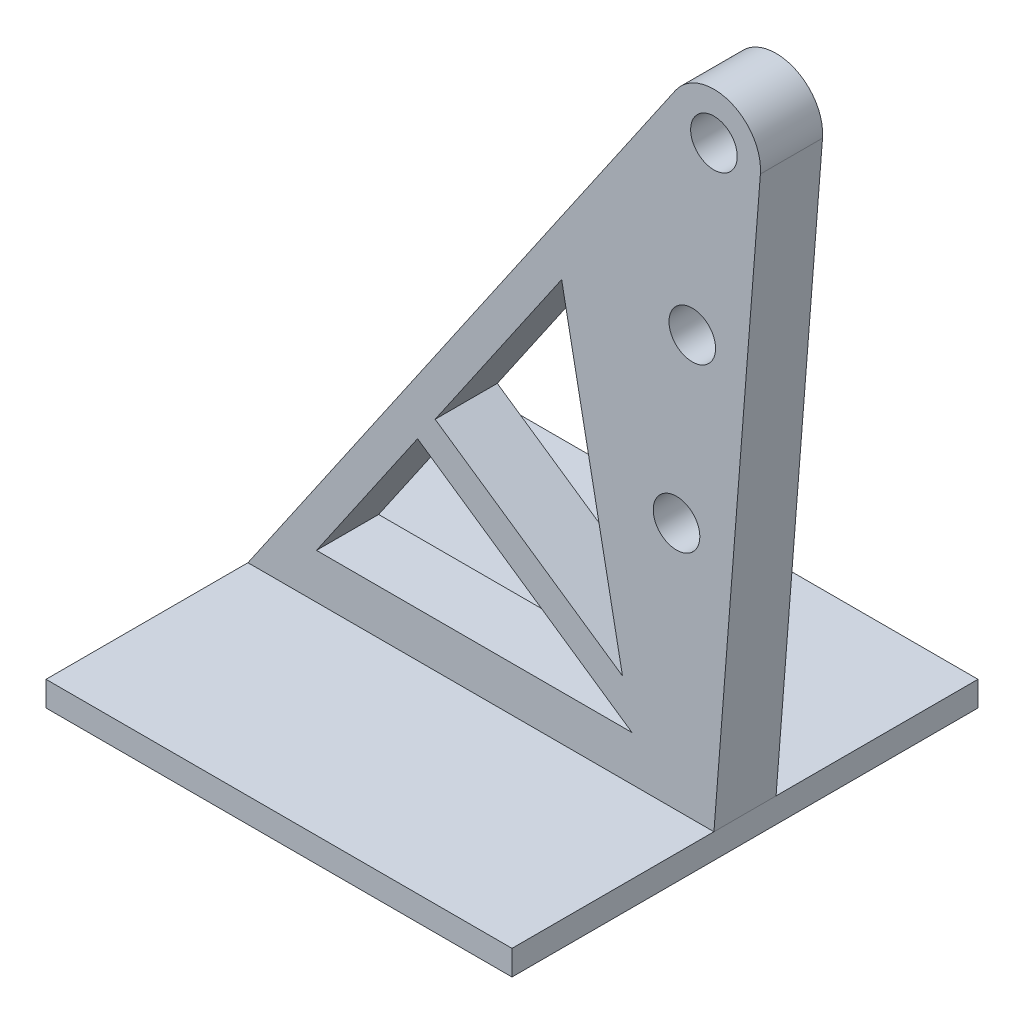
SolidWorks part; units mm, degrees
other "Markup1"
sketch "Sketch4" plane through (-7.5, 21, -7.5) normal (-0.0163, 0.004, -0.9999) x (-0.9959, 0.0889, 0.0166)
sketch "Sketch7" plane through (-7.5, 21.5, -7.5) normal (-0.0163, 0.004, -0.9999) x (-0.9959, 0.0889, 0.0166)
other "Markup2"
sketch "Sketch5" plane through (-7.5, 21, -7.5) normal (-0.0163, 0.004, -0.9999) x (-0.9959, 0.0889, 0.0166)
sketch "Sketch8" plane through (-7.5, 21.5, -7.5) normal (-0.0163, 0.004, -0.9999) x (-0.9959, 0.0889, 0.0166)
ref_plane "Front Plane" through (0, 0, 0) normal (0, 0, 1) x (1, 0, 0)
ref_plane "Top Plane" through (0, 0, 0) normal (0, 1, 0) x (1, 0, 0)
ref_plane "Right Plane" through (0, 0, 0) normal (1, 0, 0) x (0, 0, -1)
sketch "Sketch1" plane through (0, 0, 0) normal (0, 1, 0) x (1, 0, 0)
  line L1 (-7.5, -7.5) -> (7.5, -7.5)
  line L2 (-7.5, -7.5) -> (-7.5, 7.5)
  line L3 (-7.5, 7.5) -> (7.5, 7.5)
  line L4 (7.5, -7.5) -> (7.5, 7.5)
  line L5 (-7.5, -7.5) -> (7.5, 7.5) construction
  line L6 (-7.5, 7.5) -> (7.5, -7.5) construction
  point P0 (0, 0)
  dimension "D1" = 15
  dimension "D2" = 15
extrude "Boss-Extrude1" add sketch "Sketch1" along normal blind 0.8
sketch "Sketch2" plane through (0, 0, 0) normal (0, 0, 1) x (1, 0, 0)
  line L0 (0, 0) -> (0, 20) construction
  line L1 (0, 20) -> (7.5, 20) construction
  line L2 (-7.5, 0.8) -> (6.2634, 20.8489)
  line L3 (-7.5, 0.8) -> (7.5, 0.8)
  line L4 (7.5, 0.8) -> (8.9954, 19.8828)
  arc A0 (8.9954, 19.8828) -> (6.2634, 20.8489) centre (7.5, 20) ccw
  circle A1 centre (7.5, 20) radius 0.5
  dimension "D3" = 3
  dimension "D4" = 1
  dimension "D1" = 20
  dimension "D2" = 7.5
extrude "Boss-Extrude2" add sketch "Sketch2" along normal mid plane 2 contours L2 A0 L4 L3
sketch "Sketch3" plane through (0, 0, -1) normal (0, 0, -1) x (-1, 0, 0)
  circle A0 centre (-7.5, 20) radius 0.75
  dimension "D1" = 1.5
extrude "Cut-Extrude2" cut sketch "Sketch3" against normal through all
sketch "Sketch6" plane through (0, 0, 1) normal (0, 0, 1) x (1, 0, 0)
  line L0 (-2.0399, 6.9867) -> (-5.2935, 2.2473)
  line L1 (-5.2935, 2.2473) -> (4.8639, 2.2473)
  line L2 (4.8639, 2.2473) -> (-2.0399, 6.9867)
  line L3 (-7.5, 0.8) -> (6.2634, 20.8489) construction
  line L4 (-1.474, 7.8112) -> (4.5564, 3.6714)
  line L5 (4.5564, 3.6714) -> (2.598, 13.7427)
  line L6 (2.598, 13.7427) -> (-1.474, 7.8112)
  line L7 (-7.5, 0.8) -> (7.5, 0.8) construction
  circle A0 centre (6.8034, 14.3) radius 0.75
  circle A1 centre (6.2959, 8.8) radius 0.75
  circle A2 centre (7.5, 20) radius 0.75 construction
  dimension "D1" = 1
  dimension "D2" = 1
  dimension "D3" = 1
  dimension "D4" = 13.5
  dimension "D5" = 8
extrude "Cut-Extrude3" cut sketch "Sketch6" against normal blind 70
